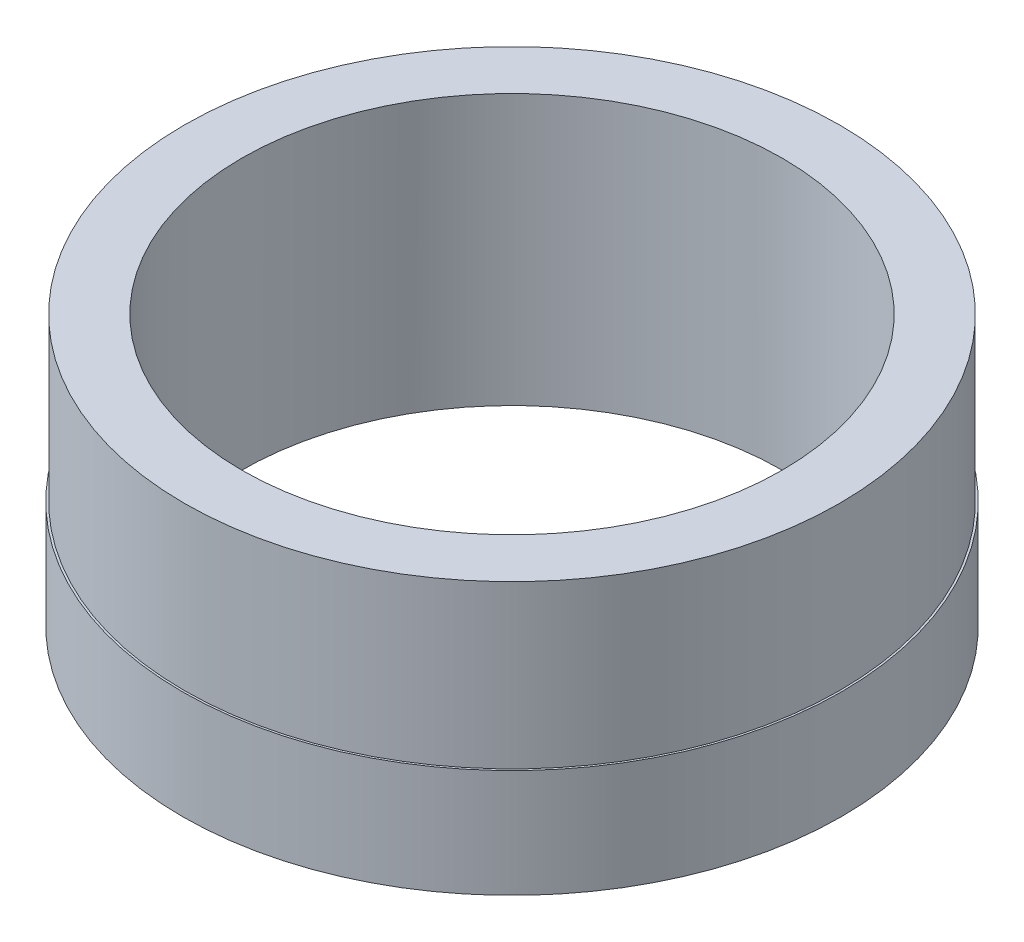
SolidWorks part; units mm, degrees
ref_plane "Спереди" through (0, 0, 0) normal (0, 0, 1) x (1, 0, 0)
ref_plane "Сверху" through (0, 0, 0) normal (0, 1, 0) x (1, 0, 0)
ref_plane "Справа" through (0, 0, 0) normal (1, 0, 0) x (0, 0, -1)
sketch "Эскиз1" plane through (0, 0, 0) normal (0, 1, 0) x (1, 0, 0)
  circle A0 centre (0, 0) radius 24.4
extrude "Бобышка-Вытянуть1" add sketch "Эскиз1" along normal blind 8
sketch "Эскиз2" plane through (0, 8, 0) normal (0, 1, 0) x (1, 0, 0)
  circle A0 centre (0, 0) radius 24.25
extrude "Бобышка-Вытянуть2" add sketch "Эскиз2" along normal blind 12
sketch "Эскиз3" plane through (0, 0, 0) normal (0, -1, 0) x (1, 0, 0)
  circle A0 centre (0, 0) radius 20
extrude "Вырез-Вытянуть1" cut sketch "Эскиз3" against normal blind 29
